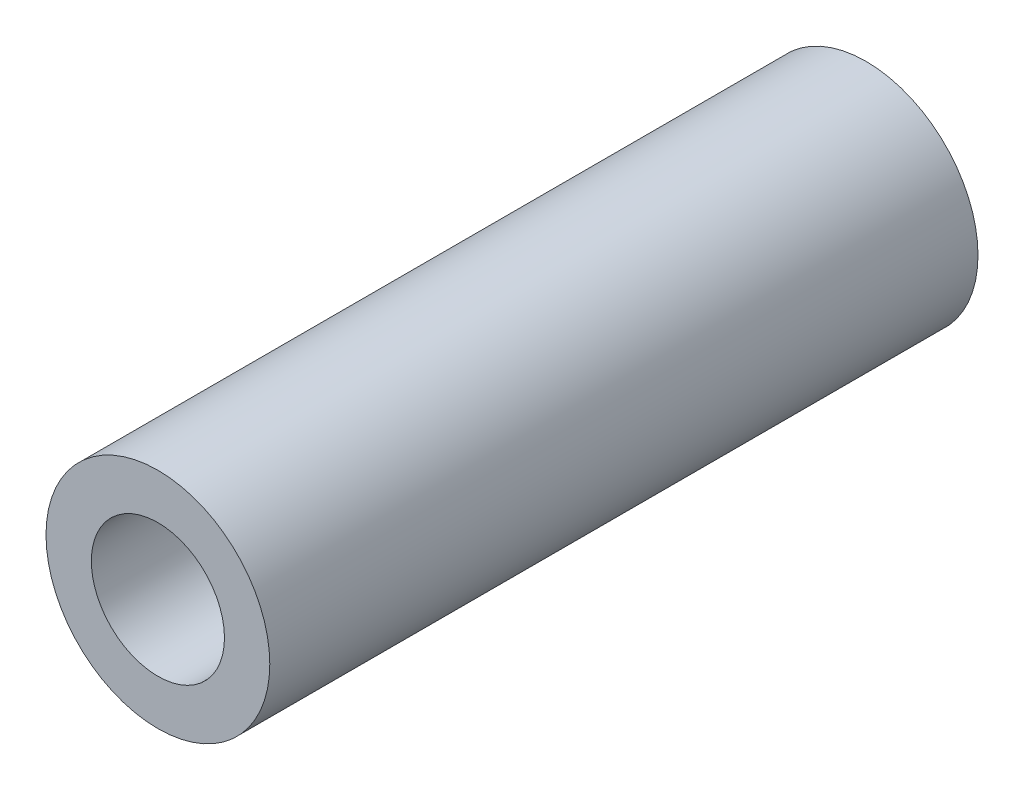
SolidWorks part; units mm, degrees
ref_plane "Front Plane" through (0, 0, 0) normal (0, 0, 1) x (1, 0, 0)
ref_plane "Top Plane" through (0, 0, 0) normal (0, 1, 0) x (1, 0, 0)
ref_plane "Right Plane" through (0, 0, 0) normal (1, 0, 0) x (0, 0, -1)
sketch "Sketch1" plane through (0, 0, 0) normal (0, 0, 1) x (1, 0, 0)
  circle A0 centre (0, 0) radius 7.9
  circle A1 centre (0, 0) radius 4.7
  dimension "D1" = 15.8
  dimension "D2" = 3.2
extrude "Boss-Extrude1" add sketch "Sketch1" against normal blind 50
